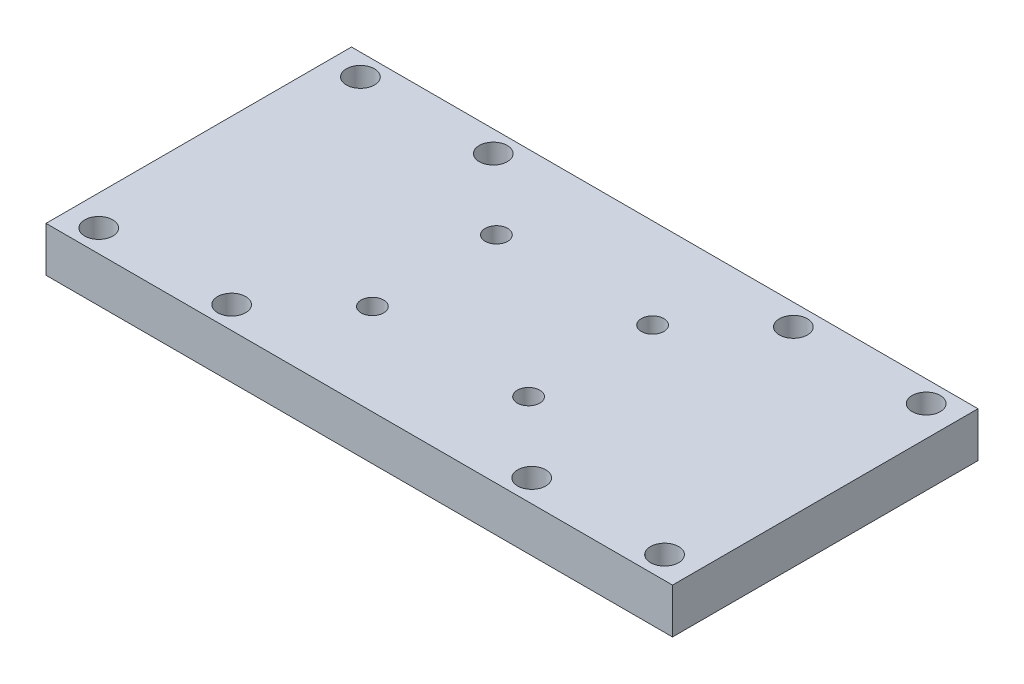
SolidWorks part; units mm, degrees
ref_plane "Front" through (0, 0, 0) normal (0, 0, 1) x (1, 0, 0)
ref_plane "Top" through (0, 0, 0) normal (0, 1, 0) x (1, 0, 0)
ref_plane "Right" through (0, 0, 0) normal (1, 0, 0) x (0, 0, -1)
sketch "Sketch1" plane through (0, 0, 0) normal (0, 1, 0) x (1, 0, 0)
  line L0 (-85.3969, 35.6145) -> (26.029, 35.6145)
  line L1 (-85.3969, 35.6145) -> (-85.3969, -18.7142)
  line L2 (-85.3969, -18.7142) -> (26.029, -18.7142)
  line L3 (26.029, 35.6145) -> (26.029, -18.7142)
  circle A0 centre (20.63, 31.8024) radius 2.5
  circle A1 centre (-2.9979, 31.8024) radius 2.5
  circle A2 centre (20.63, -14.7291) radius 2.5
  circle A3 centre (-2.9979, -14.7291) radius 2.5
  circle A4 centre (-43.5744, 19.5656) radius 2
  circle A5 centre (-15.7935, 19.5656) radius 2
  circle A6 centre (-15.7935, -2.4922) radius 2
  circle A7 centre (-43.5744, -2.4922) radius 2
  circle A8 centre (-56.37, 31.8024) radius 2.5
  circle A9 centre (-79.9979, 31.8024) radius 2.5
  circle A10 centre (-79.9979, -14.7291) radius 2.5
  circle A11 centre (-56.37, -14.7291) radius 2.5
extrude "Boss-Extrude1" add sketch "Sketch1" along normal blind 8
